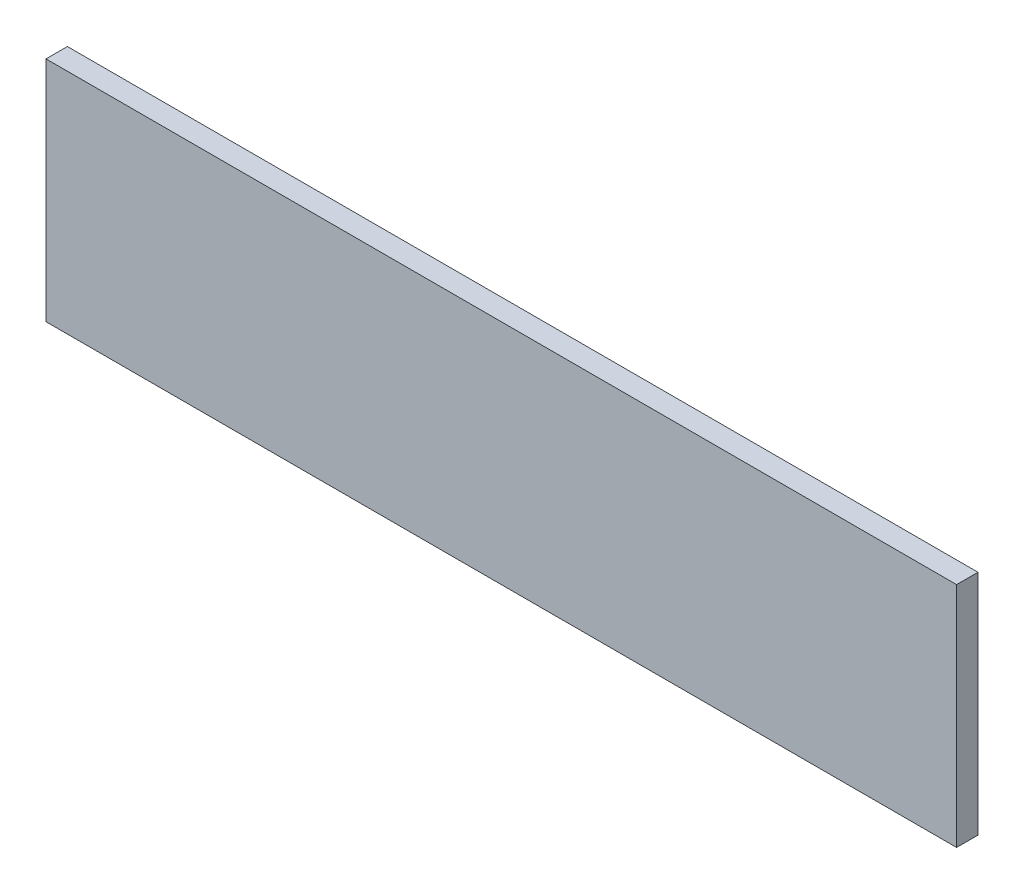
SolidWorks part; units mm, degrees
ref_plane "Front Plane" through (0, 0, 0) normal (0, 0, 1) x (1, 0, 0)
ref_plane "Top Plane" through (0, 0, 0) normal (0, 1, 0) x (1, 0, 0)
ref_plane "Right Plane" through (0, 0, 0) normal (1, 0, 0) x (0, 0, -1)
sketch "Sketch1" plane through (0, 0, 0) normal (0, 0, 1) x (1, 0, 0)
  line L1 (-254, -63.5) -> (254, -63.5)
  line L2 (-254, -63.5) -> (-254, 63.5)
  line L3 (-254, 63.5) -> (254, 63.5)
  line L4 (254, -63.5) -> (254, 63.5)
  line L5 (-254, -63.5) -> (254, 63.5) construction
  line L6 (-254, 63.5) -> (254, -63.5) construction
  point P0 (0, 0)
  dimension "D1" = 508
  dimension "D2" = 127
extrude "Boss-Extrude1" add sketch "Sketch1" along normal blind 11.938
